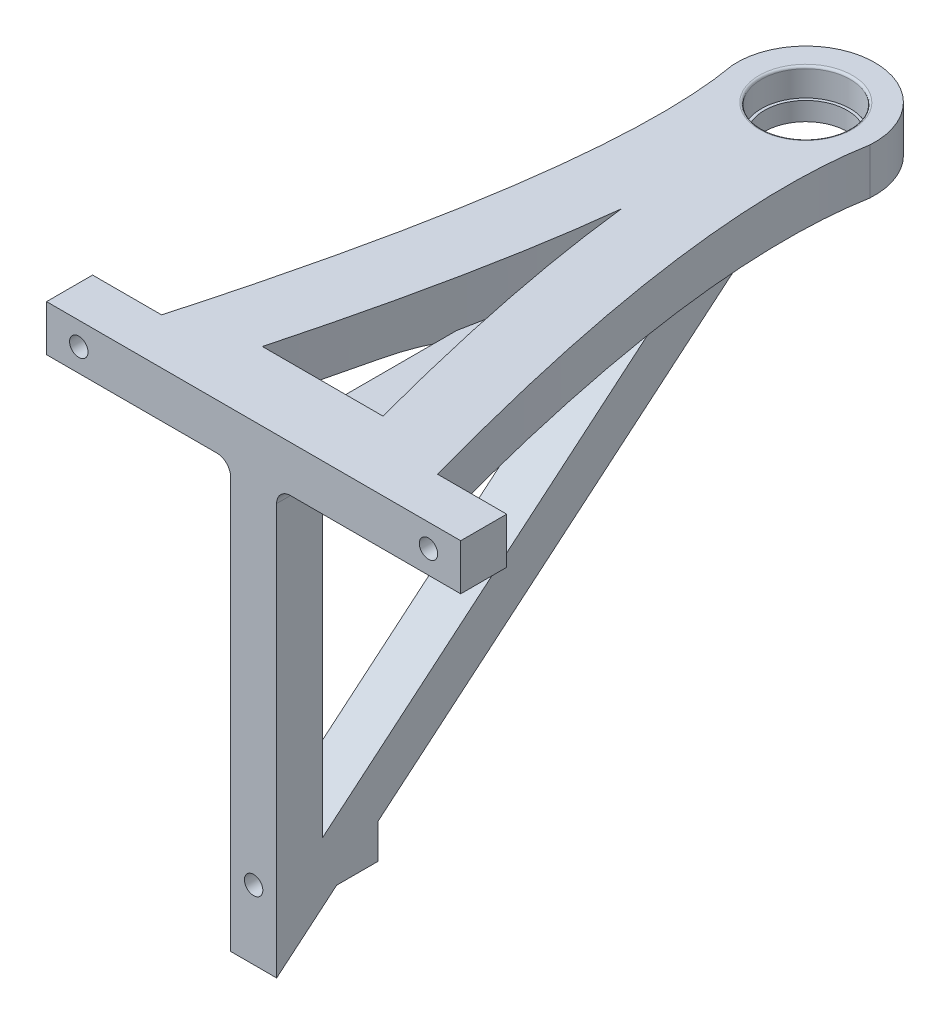
SolidWorks part; units mm, degrees
ref_plane "Спереди" through (0, 0, 0) normal (0, 0, 1) x (1, 0, 0)
ref_plane "Сверху" through (0, 0, 0) normal (0, 1, 0) x (1, 0, 0)
ref_plane "Справа" through (0, 0, 0) normal (1, 0, 0) x (0, 0, -1)
sketch "Эскиз1" plane through (0, 0, 0) normal (0, 1, 0) x (1, 0, 0)
  line L0 (0, 82.9636) -> (0, -37.0364) construction
  line L1 (31.2466, -22.0364) -> (-63.8578, -22.0364) construction
  line L2 (-28.6541, -37.0364) -> (31.2466, -37.0364) construction
  line L3 (-45, -37.0364) -> (45, -37.0364)
  line L4 (45, -37.0364) -> (45, -27.0364)
  line L5 (45, -27.0364) -> (30, -27.0364)
  line L6 (0, 82.9636) -> (0, 72.4932) construction
  line L7 (-45, -37.0364) -> (-45, -27.0364)
  line L8 (-45, -27.0364) -> (-30, -27.0364)
  line L9 (13.0938, -22.0364) -> (13.0938, -22.0364)
  line L10 (13.0938, -22.0364) -> (13.0938, -22.0364)
  line L11 (-13.0938, -22.0364) -> (13.0938, -22.0364)
  line L12 (-13.0938, -22.0364) -> (-13.0938, -22.0364)
  line L13 (-13.0938, -22.0364) -> (-13.0938, -22.0364)
  arc A0 (14.9684, 81.9907) -> (-14.9684, 81.9907) centre (0, 82.9636) ccw
  arc A1 (0, 42.893) -> (0, 42.893) centre (0, 42.893) cw
  spline S0 degree 2 poles (30, -27.0364) (8.9822, 48.4827) (14.9684, 81.9907) knots 0 0 0 0.673052 0.673052 0.673052
  spline S1 degree 2 poles (-30, -27.0364) (-8.9822, 48.4827) (-14.9684, 81.9907) knots 0 0 0 0.673052 0.673052 0.673052
  spline S2 degree 1 poles (-13.0938, -22.0364) (0, 42.893) knots 0 0 1 1 construction
  spline S3 degree 1 poles (13.0938, -22.0364) (0, 42.893) knots 0 0 1 1 construction
  spline S4 degree 3 poles (-13.0938, -22.0364) (-12.6833, -20.4919) (-11.8665, -17.3793) (-10.3174, -11.3116) (-8.5085, -3.9053) (-6.5517, 4.6626) (-4.8065, 12.9234) (-3.2743, 20.8769) (-1.9553, 28.5297) (-1.0357, 34.6525) (-0.4068, 39.417) (-0.1312, 41.7274) (0, 42.893) knots 0.040117 0.040117 0.040117 0.040117 0.061248 0.082379 0.12464 0.166901 0.209163 0.251424 0.293686 0.335947 0.357078 0.378208 0.378208 0.378208 0.378208
  spline S5 degree 3 poles (0, 42.893) (0.1312, 41.7274) (0.4068, 39.417) (1.0357, 34.6525) (1.9553, 28.5297) (3.2743, 20.8769) (4.8065, 12.9234) (6.5517, 4.6626) (8.5085, -3.9053) (10.3174, -11.3116) (11.8665, -17.3793) (12.6833, -20.4919) (13.0938, -22.0364) knots 0.040117 0.040117 0.040117 0.040117 0.061248 0.082379 0.12464 0.166901 0.209163 0.251424 0.293686 0.335947 0.357078 0.378208 0.378208 0.378208 0.378208
  dimension "D1" = 30
  dimension "D2" = 120
  dimension "D3" = 45
  dimension "D4" = 15
  dimension "D5" = 10
  dimension "D6" = 15
extrude "Бобышка-Вытянуть1" add sketch "Эскиз1" along normal blind 10
sketch "Эскиз2" plane through (0, 10, 0) normal (0, 1, 0) x (1, 0, 0)
  circle A0 centre (0, 82.9636) radius 9.65
  dimension "D1" = 19.3
extrude "Вырез-Вытянуть1" cut sketch "Эскиз2" against normal blind 6
sketch "Эскиз3" plane through (0, 4, 0) normal (0, 1, 0) x (1, 0, 0)
  circle A0 centre (0, 82.9636) radius 9
  dimension "D1" = 18
extrude "Вырез-Вытянуть2" cut sketch "Эскиз3" against normal through all
sketch "Эскиз4" plane through (0, 0, 27.0364) normal (0, 0, -1) x (-1, 0, 0)
  line L0 (30, 0) -> (45, 0) construction
  line L1 (45, 10) -> (45, 0) construction
  line L2 (-45, 10) -> (-45, 0) construction
  line L3 (-45, 0) -> (-30, 0) construction
  circle A0 centre (38, 5) radius 2
  circle A1 centre (-38, 5) radius 2
  point P8 (-45, 5)
  dimension "D2" = 7
  dimension "D3" = 4
  dimension "D4" = 7
  dimension "D1" = 5
  dimension "D5" = 5
extrude "Вырез-Вытянуть3" cut sketch "Эскиз4" against normal through all
fillet "Скругление2" radius 0.5 1 edges at (0, 10, -73.3136)
sketch "Эскиз6" plane through (0, 0, 0) normal (1, 0, 0) x (0, 0, -1)
  line L0 (72.9636, 0) -> (-37.0364, 0)
  line L1 (-37.0364, 0) -> (-37.0364, -92.301)
  line L2 (-37.0364, -92.301) -> (72.9636, 0)
  line L3 (45.4888, -10) -> (-27.0364, -10)
  line L4 (-27.0364, -10) -> (-27.0364, -70.8559)
  line L5 (-27.0364, -70.8559) -> (45.4888, -10)
  dimension "D1" = 110
  dimension "D2" = 40
  dimension "D3" = 10
extrude "Бобышка-Вытянуть3" add sketch "Эскиз6" along normal blind 5 and the other way blind 5
fillet "Скругление3" radius 3 3 edges
fillet "Скругление4" radius 3 1 edges at (5, 0, -42.5288)
fillet "Скругление5" radius 3 2 edges at (-5, 0, -42.5288)
fillet "Скругление6" radius 3 2 edges
sketch "Эскиз8" plane through (0, 0, 37.0364) normal (0, 0, 1) x (1, 0, 0)
  line L0 (-5, -3) -> (-5, -92.301) construction
  line L1 (5, -73.2413) -> (-5, -73.2413)
  line L2 (5, -73.2413) -> (5, -81.3606)
  line L3 (5, -81.3606) -> (-5, -81.3606)
  line L4 (-5, -73.2413) -> (-5, -81.3606)
  line L5 (5, -73.2413) -> (-5, -81.3606) construction
  line L6 (5, -81.3606) -> (-5, -73.2413) construction
  point P0 (0, -77.301)
extrude "Бобышка-Вытянуть5" add sketch "Эскиз8" against normal blind 22
sketch "Эскиз7" plane through (0, 0, 37.0364) normal (0, 0, 1) x (1, 0, 0)
  line L0 (-5, -92.301) -> (5, -92.301) construction
  circle A0 centre (0, -77.301) radius 2
  dimension "D1" = 4
  dimension "D2" = 15
extrude "Вырез-Вытянуть4" cut sketch "Эскиз7" against normal through all
